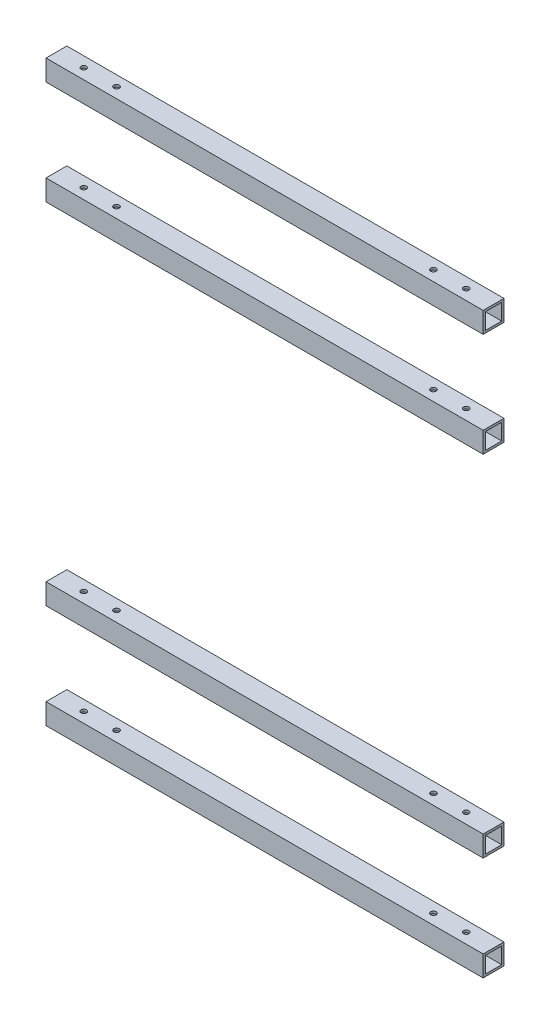
SolidWorks part; units mm, degrees
material "6061 Alloy"
ref_plane "Front Plane" through (0, 0, 0) normal (0, 0, 1) x (1, 0, 0)
ref_plane "Top Plane" through (0, 0, 0) normal (0, 1, 0) x (1, 0, 0)
ref_plane "Right Plane" through (0, 0, 0) normal (1, 0, 0) x (0, 0, -1)
sketch "Sketch1" plane through (0, 0, 0) normal (0, 0, 1) x (1, 0, 0)
  line L0 (0, 0) -> (400, 0)
  line L1 (0, -510) -> (400, -510)
  line L2 (0, -95) -> (400, -95)
  line L3 (400, -255) -> (513.7405, -255) construction
  line L4 (0, -415) -> (400, -415)
  dimension "D1" = 95
  dimension "D2" = 400
  dimension "D3" = 160
  dimension "D4" = 95
other "Al tube square AL TUBE 0.75 SQR X 0.083 WALL(1)"
ref_plane "Plane1" through (0, -415, 0) normal (1, 0, 0) x (0, 1, 0)
sketch "Sketch11" plane through (0, -415, 0) normal (1, 0, 0) x (0, 1, 0)
  line L0 (-7.4168, -7.4168) -> (-7.4168, 7.4168)
  line L1 (7.4168, 7.4168) -> (-7.4168, 7.4168)
  line L2 (7.4168, 7.4168) -> (7.4168, -7.4168)
  line L3 (-7.4168, -7.4168) -> (7.4168, -7.4168)
  line L4 (-9.525, -9.525) -> (9.525, -9.525)
  line L5 (-9.525, -9.525) -> (-9.525, 9.525)
  line L6 (9.525, 9.525) -> (-9.525, 9.525)
  line L7 (9.525, 9.525) -> (9.525, -9.525)
  line L8 (0, -7.4168) -> (0, -9.525) construction
  line L9 (0, -7.4168) -> (0, 7.4168) construction
  line L10 (0, 7.4168) -> (0, 9.525) construction
  line L11 (9.525, 0) -> (7.4168, 0) construction
  line L12 (7.4168, 0) -> (-7.4168, 0) construction
  line L13 (-7.4168, 0) -> (-9.525, 0) construction
  point P14 (0, 0)
  point P17 (0, 0)
  dimension "Thickness" = 2.1082
  dimension "V_leg" = 19.05
  dimension "H_leg" = 19.05
sketch "Sketch12" plane through (0, -519.525, 0) normal (0, -1, 0) x (1, 0, 0)
  line L1 (0, 9.525) -> (0, -9.525) construction
  line L2 (200, 9.525) -> (200, 49.9408) construction
  line L3 (400, 9.525) -> (0, 9.525) construction
  circle A0 centre (25, 0) radius 2.5
  circle A1 centre (55, 0) radius 2.5
  circle A2 centre (345, 0) radius 2.5
  circle A3 centre (375, 0) radius 2.5
  dimension "D1" = 5
  dimension "D3" = 30
  dimension "D2" = 25
extrude "Cut-Extrude1" cut sketch "Sketch12" against normal through all
sketch "Sketch13" plane through (0, -424.525, 0) normal (0, -1, 0) x (1, 0, 0)
  circle A0 centre (25, 0) radius 2.5
  circle A1 centre (55, 0) radius 2.5
  circle A2 centre (345, 0) radius 2.5
  circle A3 centre (375, 0) radius 2.5
extrude "Cut-Extrude2" cut sketch "Sketch13" against normal up to surface (339.05 mm away) up to face at (200, -85.475, 0)
